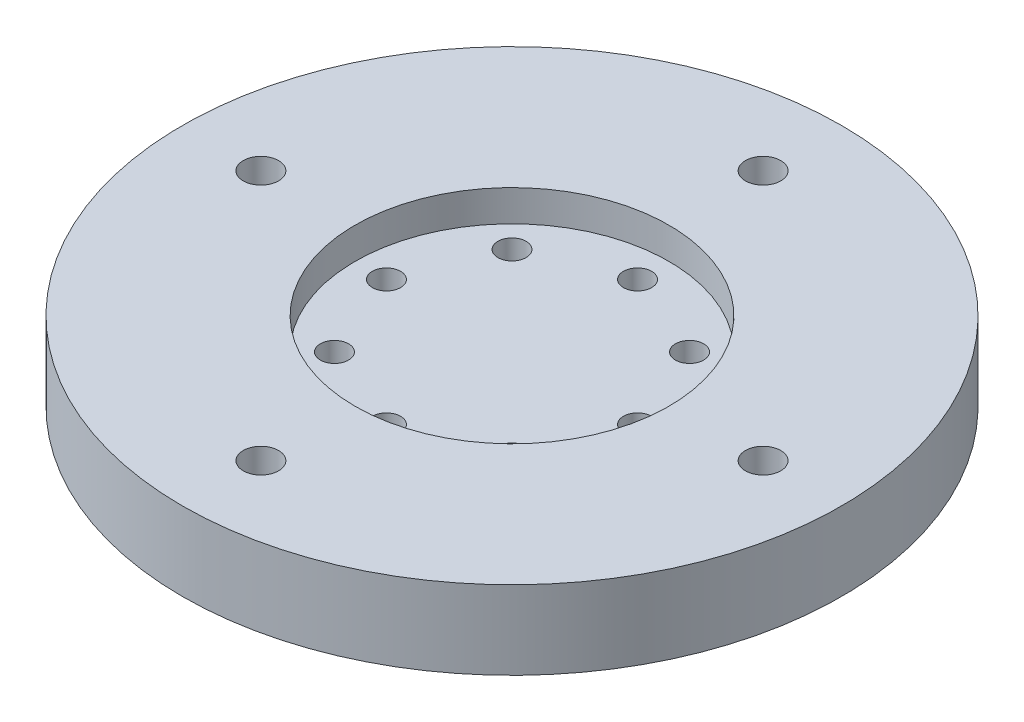
SolidWorks part; units mm, degrees
ref_plane "정면" through (0, 0, 0) normal (0, 0, 1) x (1, 0, 0)
ref_plane "윗면" through (0, 0, 0) normal (0, 1, 0) x (1, 0, 0)
ref_plane "우측면" through (0, 0, 0) normal (1, 0, 0) x (0, 0, -1)
sketch "스케치1" plane through (0, 0, 0) normal (0, 1, 0) x (1, 0, 0)
  circle A0 centre (0, 0) radius 21
  dimension "D1" = 42
extrude "보스-돌출1" add sketch "스케치1" along normal blind 5
sketch "스케치2" plane through (0, 5, 0) normal (0, 1, 0) x (1, 0, 0)
  circle A0 centre (0, 0) radius 10
  dimension "D1" = 20
extrude "컷-돌출1" cut sketch "스케치2" against normal blind 2
sketch "스케치3" plane through (0, 3, 0) normal (0, 1, 0) x (1, 0, 0)
  line L0 (0, 0) -> (8, 0) construction
  line L1 (8, 0) -> (0, -8) construction
  line L2 (0, -8) -> (-8, 0) construction
  line L3 (-8, 0) -> (0, 8) construction
  line L4 (0, 8) -> (8, 0) construction
  line L5 (8, 0) -> (0, 0) construction
  line L6 (0, 0) -> (5.6569, 5.6569) construction
  line L7 (5.6569, 5.6569) -> (5.6569, -5.6569) construction
  line L8 (5.6569, -5.6569) -> (-5.6569, -5.6569) construction
  line L9 (-5.6569, -5.6569) -> (-5.6569, 5.6569) construction
  line L10 (-5.6569, 5.6569) -> (5.6569, 5.6569) construction
  line L11 (0, 8) -> (0, -8) construction
  circle A0 centre (0, 0) radius 8 construction
  circle A1 centre (5.6569, 5.6569) radius 0.9
  circle A2 centre (8, 0) radius 0.9
  circle A3 centre (0, 8) radius 0.9
  circle A4 centre (5.6569, -5.6569) radius 0.9
  circle A5 centre (0, -8) radius 0.9
  circle A6 centre (-5.6569, -5.6569) radius 0.9
  circle A7 centre (-8, 0) radius 0.9
  circle A8 centre (-5.6569, 5.6569) radius 0.9
  dimension "D1" = 1.8
  dimension "D2" = 1.8
  dimension "D3" = 1.8
extrude "컷-돌출2" cut sketch "스케치3" against normal up to surface (3 mm away) up to face at (0, 0, 21)
sketch "스케치4" plane through (0, 0, 0) normal (0, -1, 0) x (1, 0, 0)
  line L0 (0, -16) -> (0, 16) construction
  line L1 (0, 16) -> (16, 0) construction
  line L2 (16, 0) -> (-16, 0) construction
  line L3 (-16, 0) -> (0, -16) construction
  circle A0 centre (0, 0) radius 16 construction
  circle A1 centre (0, -16) radius 1.125
  circle A2 centre (-16, 0) radius 1.125
  circle A3 centre (0, 16) radius 1.125
  circle A4 centre (16, 0) radius 1.125
  dimension "D1" = 32
  dimension "D2" = 2.25
  dimension "D3" = 2.25
  dimension "D4" = 2.25
  dimension "D5" = 2.25
extrude "컷-돌출3" cut sketch "스케치4" against normal up to surface (5 mm away) up to face at (0, 5, 10)
